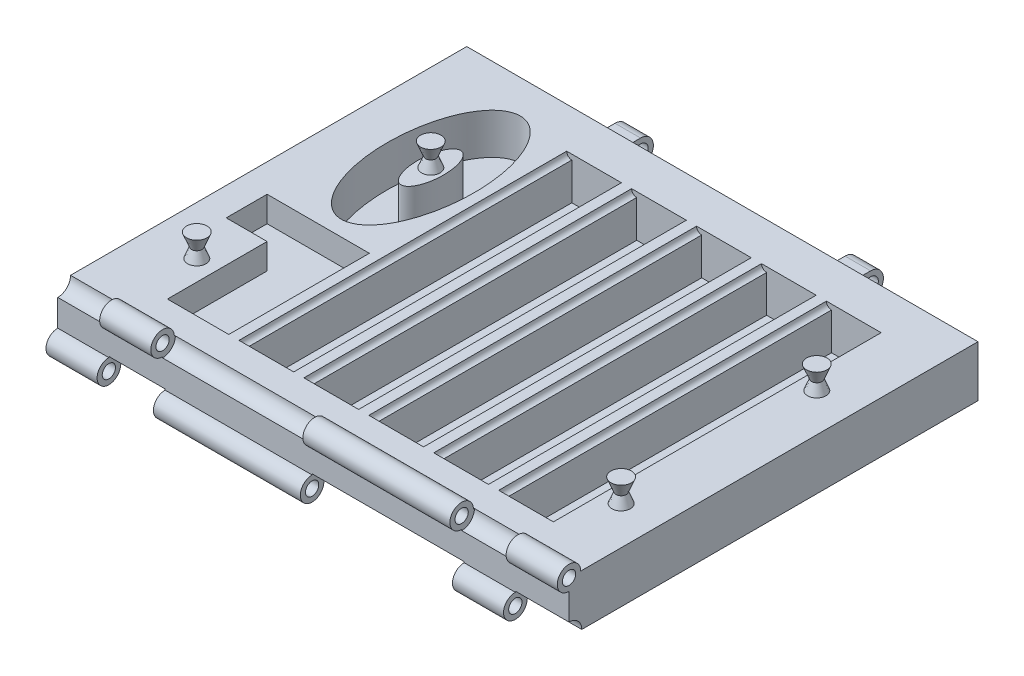
SolidWorks part; units mm, degrees
ref_plane "Front Plane" through (0, 0, 0) normal (0, 0, 1) x (1, 0, 0)
ref_plane "Top Plane" through (0, 0, 0) normal (0, 1, 0) x (1, 0, 0)
ref_plane "Right Plane" through (0, 0, 0) normal (1, 0, 0) x (0, 0, -1)
sketch "Sketch1" plane through (0, 0, 0) normal (0, 1, 0) x (1, 0, 0)
  line L0 (0, 0) -> (254, 0)
  line L1 (254, 0) -> (254, 203.2)
  line L2 (254, 203.2) -> (0, 203.2)
  line L3 (0, 203.2) -> (0, 0)
extrude "Boss-Extrude2" add sketch "Sketch1" along normal blind 25.4
sketch "Sketch2" plane through (0, 25.4, 0) normal (0, 1, 0) x (1, 0, 0)
  line L0 (254, 0) -> (254, 203.2) construction
  line L1 (0, 203.2) -> (0, 0) construction
  line L2 (0, 0) -> (0, 20.193)
  line L4 (72.39, 183.007) -> (72.39, 20.193)
  line L5 (72.39, 20.193) -> (97.028, 20.193)
  line L6 (97.028, 20.193) -> (97.028, 183.007)
  line L7 (97.028, 183.007) -> (72.39, 183.007)
  line L9 (104.648, 183.007) -> (104.648, 20.193)
  line L10 (104.648, 20.193) -> (129.286, 20.193)
  line L11 (129.286, 20.193) -> (129.286, 183.007)
  line L12 (129.286, 183.007) -> (104.648, 183.007)
  line L14 (136.906, 183.007) -> (136.906, 20.193)
  line L15 (136.906, 20.193) -> (161.544, 20.193)
  line L16 (161.544, 20.193) -> (161.544, 183.007)
  line L17 (161.544, 183.007) -> (136.906, 183.007)
  line L19 (169.164, 183.007) -> (169.164, 20.193)
  line L20 (169.164, 20.193) -> (193.802, 20.193)
  line L21 (193.802, 20.193) -> (193.802, 183.007)
  line L22 (193.802, 183.007) -> (169.164, 183.007)
  line L24 (201.422, 183.007) -> (201.422, 20.193)
  line L25 (201.422, 20.193) -> (226.06, 20.193)
  line L26 (226.06, 20.193) -> (226.06, 183.007)
  line L27 (226.06, 183.007) -> (201.422, 183.007)
  dimension "D1" = 7.62
  dimension "D2" = 27.94
  dimension "D3" = 24.638
  dimension "D4" = 24.638
  dimension "D5" = 24.638
  dimension "D6" = 24.638
  dimension "D7" = 24.638
  dimension "D8" = 7.62
  dimension "D9" = 7.62
  dimension "D10" = 7.62
extrude "Cut-Extrude1" cut sketch "Sketch2" against normal blind 20.955 contours L6 L7 L4 L5 | L11 L12 L9 L10 | L16 L17 L14 L15 | L21 L22 L19 L20 | L26 L27 L24 L25
sketch "Sketch3" plane through (0, 0, -183.007) normal (0, 0, 1) x (1, 0, 0)
  circle A0 centre (72.39, 25.4) radius 2.54
  circle A1 centre (104.648, 25.4) radius 2.54
  circle A2 centre (136.906, 25.4) radius 2.54
  circle A3 centre (169.164, 25.4) radius 2.54
  circle A4 centre (201.422, 25.4) radius 2.54
extrude "Cut-Extrude2" cut sketch "Sketch3" along normal blind 162.814
sketch "Sketch4" plane through (254, 0, 0) normal (1, 0, 0) x (0, 0, -1)
  circle A0 centre (0, 25.4) radius 6.35
extrude "Cut-Extrude3" cut sketch "Sketch4" against normal blind 330.708
sketch "Sketch5" plane through (254, 0, 0) normal (1, 0, 0) x (0, 0, -1)
  line L0 (0, 19.558) -> (0, 17.6422)
  line L1 (0, 19.05) -> (0, 0) construction
  line L2 (0, 17.6422) -> (6.6323, 19.558)
  line L3 (6.6323, 19.558) -> (7.5821, 25.4)
  line L4 (6.35, 25.4) -> (203.2, 25.4) construction
  line L5 (7.5821, 25.4) -> (5.842, 25.4)
  circle A0 centre (0, 25.4) radius 5.842
  circle A1 centre (0, 25.4) radius 3.302
  arc M2 (6.35, 25.4) -> (0, 19.05) centre (0, 25.4) cw
extrude "Boss-Extrude3" add sketch "Sketch5" against normal blind 25.4 contours A0 L0 L5 M2 | A0 A1
sketch "Sketch6" plane through (0, 0, 0) normal (0, 0, 1) x (1, 0, 0)
  line L0 (0, 19.05) -> (26.67, 19.05)
  line L1 (228.6, 19.05) -> (0, 19.05) construction
ref_plane "Plane1" through (26.67, 0, 0) normal (-1, 0, 0) x (0, 0, 1)
sketch "Sketch7" plane through (26.67, 0, 0) normal (-1, 0, 0) x (0, 0, 1)
  line L0 (-5.842, 25.4) -> (-6.9029, 25.4)
  line L1 (-203.2, 25.4) -> (-6.35, 25.4) construction
  line L2 (-6.9029, 25.4) -> (-6.3725, 22.098)
  line L3 (-6.3725, 22.098) -> (-4.097, 19.395)
  line L4 (-4.097, 19.395) -> (0, 18.4548)
  line L5 (0, 19.05) -> (0, 0) construction
  line L6 (0, 18.4548) -> (0, 19.558)
  circle A0 centre (0, 25.4) radius 5.842
  circle A1 centre (0, 25.4) radius 3.302
extrude "Boss-Extrude4" add sketch "Sketch7" against normal blind 25.4 contours A0 L0 L2 L3 L4 L6 | A0 A1
sketch "Sketch8" plane through (0, 0, 0) normal (0, 0, 1) x (1, 0, 0)
  line L0 (254, 19.558) -> (200.66, 19.558)
ref_plane "Plane2" through (200.66, 0, 0) normal (1, 0, 0) x (0, 0, -1)
sketch "Sketch9" plane through (200.66, 0, 0) normal (1, 0, 0) x (0, 0, -1)
  line L0 (5.842, 25.4) -> (7.2961, 25.4)
  line L1 (5.842, 25.4) -> (203.2, 25.4) construction
  line L2 (7.2961, 25.4) -> (5.842, 20.1623)
  line L3 (5.842, 20.1623) -> (2.519, 18.9221)
  line L4 (2.519, 18.9221) -> (0, 18.4627)
  line L5 (0, 19.558) -> (0, 0) construction
  line L6 (0, 18.4627) -> (0, 19.558)
  circle A0 centre (0, 25.4) radius 3.302
  circle A1 centre (0, 25.4) radius 5.842
extrude "Boss-Extrude5" add sketch "Sketch9" against normal blind 73.025 contours A1 L6 L4 L3 L2 L0 | A1 A0
sketch "Sketch11" plane through (254, 0, 0) normal (1, 0, 0) x (0, 0, -1)
  circle A0 centre (0, 0) radius 6.35
extrude "Cut-Extrude4" cut sketch "Sketch11" against normal blind 271.907
sketch "Sketch12" plane through (0, 0, 0) normal (-1, 0, 0) x (0, 0, 1)
  line L0 (0, 5.842) -> (0, 7.5149)
  line L1 (0, 19.05) -> (0, 6.35) construction
  line L2 (0, 7.5149) -> (-5.842, 5.5619)
  line L3 (-5.842, 5.5619) -> (-7.1379, 1.822)
  line L4 (-7.1379, 1.822) -> (-7.1379, 0)
  line L5 (-203.2, 0) -> (-6.35, 0) construction
  line L6 (-7.1379, 0) -> (-5.842, 0)
  circle A0 centre (0, 0) radius 5.842
  circle A1 centre (0, 0) radius 3.302
  arc M2 (-6.35, 0) -> (0, 6.35) centre (0, 0) cw
extrude "Boss-Extrude6" add sketch "Sketch12" against normal blind 25.4 contours A0 L0 L6 M2 | A0 A1
sketch "Sketch13" plane through (0, 0, 0) normal (0, 0, 1) x (1, 0, 0)
  line L0 (0, 5.842) -> (53.34, 5.842)
  line L1 (25.4, 5.842) -> (0, 5.842) construction
ref_plane "Plane3" through (53.34, 0, 0) normal (-1, 0, 0) x (0, 0, 1)
sketch "Sketch14" plane through (53.34, 0, 0) normal (-1, 0, 0) x (0, 0, 1)
  line L0 (0, 5.842) -> (0, 7.342)
  line L1 (0, 19.05) -> (0, 5.842) construction
  line L2 (0, 7.342) -> (-6.417, 5.3479)
  line L3 (-6.417, 5.3479) -> (-7.9708, 0)
  line L4 (-203.2, 0) -> (-5.842, 0) construction
  line L5 (-7.9708, 0) -> (-5.842, 0)
  circle A0 centre (0, 0) radius 5.842
  circle A1 centre (0, 0) radius 3.302
extrude "Boss-Extrude7" add sketch "Sketch14" against normal blind 73.025 contours A0 L0 L2 L3 L5 | A0 A1
sketch "Sketch16" plane through (0, 0, 0) normal (0, 0, 1) x (1, 0, 0)
  line L0 (254, 6.35) -> (227.33, 6.35)
  line L1 (126.365, 6.35) -> (254, 6.35) construction
ref_plane "Plane4" through (227.33, 0, 0) normal (1, 0, 0) x (0, 0, -1)
sketch "Sketch17" plane through (227.33, 0, 0) normal (1, 0, 0) x (0, 0, -1)
  line L0 (0, 5.842) -> (0, 7.4374)
  line L1 (0, 19.558) -> (0, 6.35) construction
  line L2 (0, 7.4374) -> (5.842, 4.855)
  line L3 (5.842, 4.855) -> (6.7288, 0)
  line L4 (6.35, 0) -> (203.2, 0) construction
  line L5 (6.7288, 0) -> (5.842, 0)
  circle A0 centre (0, 0) radius 3.302
  circle A1 centre (0, 0) radius 5.842
extrude "Boss-Extrude8" add sketch "Sketch17" against normal blind 25.4 contours A1 L5 L3 L2 L0 | A1 A0
sketch "Sketch19" plane through (0, 25.4, 0) normal (0, 1, 0) x (1, 0, 0)
  line L0 (72.39, 20.193) -> (64.77, 20.193)
  line L1 (64.77, 20.193) -> (64.77, 90.043)
  line L2 (64.77, 20.193) -> (34.29, 20.193)
  line L3 (34.29, 20.193) -> (34.29, 69.723)
  line L4 (34.29, 69.723) -> (13.97, 69.723)
  line L5 (13.97, 69.723) -> (13.97, 90.043)
  line L6 (13.97, 90.043) -> (64.77, 90.043)
extrude "Cut-Extrude5" cut sketch "Sketch19" against normal blind 12.7 contours L6 L5 L4 L3 L2 L1
sketch "Sketch20" plane through (0, 25.4, 0) normal (0, 1, 0) x (1, 0, 0)
  line L0 (72.39, 183.007) -> (72.39, 20.193) construction
  ellipse E0 centre (43.18, 142.1639) end of major axis (43.18, 97.7139) minor radius 21.59
  ellipse E1 centre (43.18, 142.1639) end of major axis (43.18, 156.9721) minor radius 6.35
  dimension "D1" = 0
  dimension "D2" = 7.62
extrude "Cut-Extrude6" cut sketch "Sketch20" against normal blind 20.32
sketch "Sketch24" plane through (0, 25.4, 0) normal (0, 1, 0) x (1, 0, 0)
  line L0 (254, 5.842) -> (254, 203.2) construction
  circle A0 centre (24.13, 44.958) radius 2.54
  circle A1 centre (234.95, 44.958) radius 2.54
  dimension "D1" = 19.05
extrude "Boss-Extrude9" add sketch "Sketch24" along normal blind 5.08
sketch "Sketch25" plane through (0, 25.4, 0) normal (0, 1, 0) x (1, 0, 0)
  circle A0 centre (43.18, 142.1639) radius 2.54
  circle A1 centre (234.95, 142.1639) radius 2.54
extrude "Boss-Extrude10" add sketch "Sketch25" along normal blind 5.08
sketch "Sketch27" plane through (0, 0, -203.2) normal (0, 0, -1) x (-1, 0, 0)
  line L0 (-254, 0) -> (-177.8, 0)
  line L1 (-254, 0) -> (0, 0) construction
ref_plane "Plane5" through (177.8, 0, 0) normal (1, 0, 0) x (0, 0, -1)
sketch "Sketch28" plane through (177.8, 0, 0) normal (1, 0, 0) x (0, 0, -1)
  line L0 (203.2, 12.7) -> (203.2, 19.05)
  line L1 (203.2, 25.4) -> (203.2, 0) construction
  line L2 (203.2, 12.7) -> (203.2, 6.35)
  line L3 (203.2, 19.05) -> (213.36, 19.05)
  line L4 (203.2, 6.35) -> (213.36, 6.35)
  circle A0 centre (213.36, 12.7) radius 6.35
extrude "Boss-Extrude11" add sketch "Sketch28" along normal blind 12.7 contours A0 L3 L0 L2 L4 | A0
sketch "Sketch29" plane through (0, 0, -203.2) normal (0, 0, -1) x (-1, 0, 0)
  line L0 (0, 0) -> (-76.2, 0)
  line L1 (-254, 0) -> (0, 0) construction
ref_plane "Plane6" through (76.2, 0, 0) normal (1, 0, 0) x (0, 0, -1)
sketch "Sketch30" plane through (76.2, 0, 0) normal (1, 0, 0) x (0, 0, -1)
  line L0 (203.2, 19.05) -> (203.2, 6.35)
  line L1 (203.2, 6.35) -> (213.36, 6.35)
  line L2 (213.36, 19.05) -> (203.2, 19.05)
  circle A0 centre (213.36, 12.7) radius 6.35
extrude "Boss-Extrude12" add sketch "Sketch30" against normal blind 12.7 contours A0 L2 L0 L1 | A0
sketch "Sketch31" plane through (190.5, 0, 0) normal (1, 0, 0) x (0, 0, -1)
  circle A0 centre (213.36, 12.7) radius 3.81
extrude "Cut-Extrude7" cut sketch "Sketch31" against normal blind 150.114
fillet "Fillet1" radius 5.08 4 edges at (184.15, 6.35, -203.2) (69.85, 6.35, -203.2) (69.85, 19.05, -203.2) (184.15, 19.05, -203.2)
sketch "Sketch33" plane through (0, 30.48, 0) normal (0, 1, 0) x (1, 0, 0)
  line L0 (234.95, 142.1639) -> (237.49, 142.1639)
  circle A0 centre (234.95, 142.1639) radius 2.54 construction
ref_plane "Plane7" through (0, 0, -142.1639) normal (0, 0, -1) x (-1, 0, 0)
sketch "Sketch34" plane through (0, 0, -142.1639) normal (0, 0, -1) x (-1, 0, 0)
  line L0 (-234.95, 24.13) -> (-234.95, 36.83)
  line L1 (-234.95, 30.48) -> (-237.49, 30.48) construction
  line L2 (-234.95, 36.83) -> (-240.03, 36.83)
  line L3 (-240.03, 36.83) -> (-237.49, 30.48)
  line L4 (-237.49, 30.48) -> (-234.95, 30.48)
  line L5 (-234.95, 24.13) -> (-240.03, 24.13)
  line L6 (-240.03, 24.13) -> (-237.49, 30.48)
revolve "Revolve1" add sketch "Sketch34" angle 360 about L0
sketch "Sketch35" plane through (0, 0, -142.1639) normal (0, 0, -1) x (-1, 0, 0)
  line L0 (-43.18, 24.13) -> (-43.18, 36.83)
  line L1 (-40.64, 30.48) -> (-45.72, 30.48) construction
  line L2 (-43.18, 30.48) -> (-40.64, 30.48)
  line L3 (-43.18, 36.83) -> (-38.1, 36.83)
  line L4 (-40.64, 30.48) -> (-38.1, 36.83)
  line L5 (-40.64, 30.48) -> (-38.1, 24.13)
  line L6 (-43.18, 24.13) -> (-38.1, 24.13)
revolve "Revolve2" add sketch "Sketch35" angle 360 about L0
sketch "Sketch36" plane through (0, 30.48, 0) normal (0, 1, 0) x (1, 0, 0)
  line L0 (234.95, 44.958) -> (234.95, 42.418)
  circle A0 centre (234.95, 44.958) radius 2.54 construction
ref_plane "Plane9" through (0, 0, -44.958) normal (0, 0, -1) x (-1, 0, 0)
sketch "Sketch38" plane through (0, 0, -44.958) normal (0, 0, -1) x (-1, 0, 0)
  line L0 (-234.95, 30.48) -> (-232.41, 30.48)
  line L1 (-237.49, 30.48) -> (-232.41, 30.48) construction
  line L2 (-232.41, 30.48) -> (-229.87, 36.83)
  line L3 (-229.87, 36.83) -> (-234.95, 36.83)
  line L4 (-229.87, 36.83) -> (-240.03, 36.83) construction
  line L5 (-234.95, 36.83) -> (-234.95, 24.13)
  line L6 (-229.87, 24.13) -> (-234.95, 24.13)
  line L7 (-232.41, 30.48) -> (-229.87, 24.13)
revolve "Revolve3" add sketch "Sketch38" angle 360 about L5
sketch "Sketch39" plane through (0, 0, -44.958) normal (0, 0, -1) x (-1, 0, 0)
  line L0 (-24.13, 30.48) -> (-21.59, 30.48)
  line L1 (-21.59, 30.48) -> (-26.67, 30.48) construction
  line L2 (-24.13, 24.13) -> (-24.13, 36.83)
  line L3 (-24.13, 36.83) -> (-19.05, 36.83)
  line L4 (-21.59, 30.48) -> (-19.05, 36.83)
  line L5 (-24.13, 24.13) -> (-19.05, 24.13)
  line L6 (-21.59, 30.48) -> (-19.05, 24.13)
revolve "Revolve7" add sketch "Sketch39" angle 360 about L2
